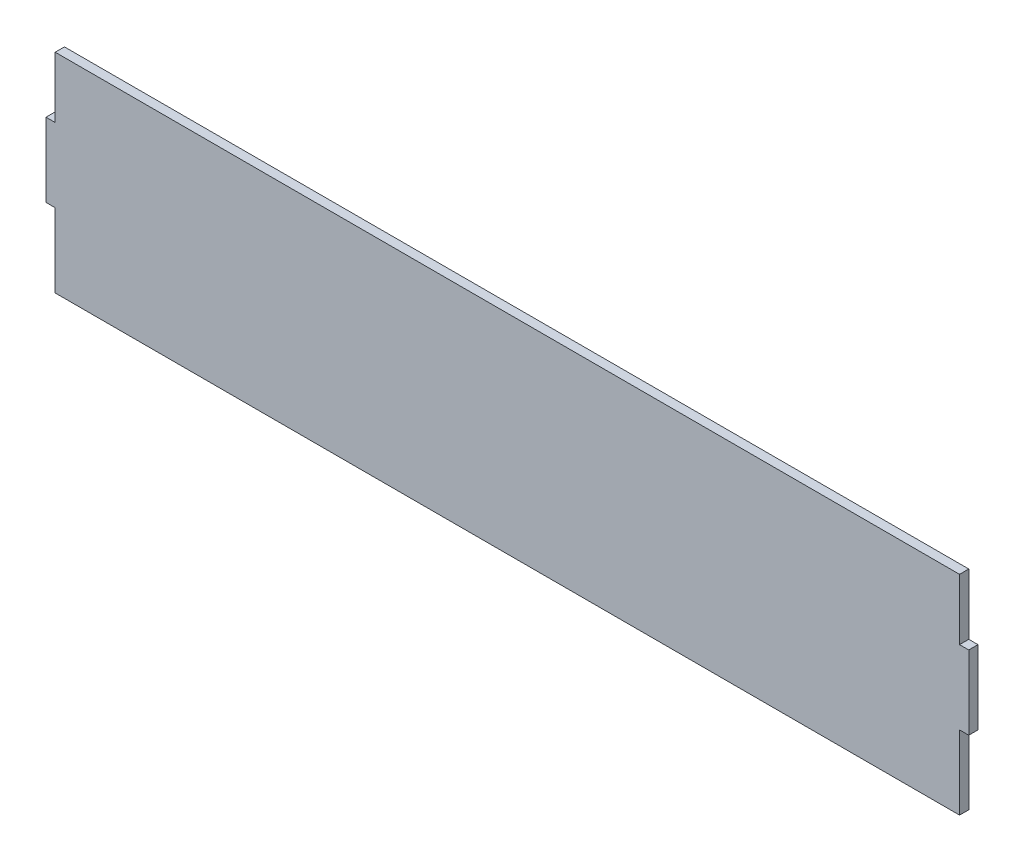
SolidWorks part; units mm, degrees
material "PMMA"
ref_plane "Plan de face" through (0, 0, 0) normal (0, 0, 1) x (1, 0, 0)
ref_plane "Plan de dessus" through (0, 0, 0) normal (0, 1, 0) x (1, 0, 0)
ref_plane "Plan de droite" through (0, 0, 0) normal (1, 0, 0) x (0, 0, -1)
sketch "Esquisse1" plane through (0, 0, 0) normal (0, 0, 1) x (1, 0, 0)
  line L0 (5, 0) -> (5, 40)
  line L1 (5, 0) -> (495, 0)
  line L2 (0, 40) -> (0, 80)
  line L3 (5, 113) -> (495, 113)
  line L5 (5, 40) -> (0, 40)
  line L6 (0, 40) -> (0, 80)
  line L7 (0, 80) -> (5, 80)
  line L8 (5, 80) -> (5, 113)
  line L9 (495, 0) -> (495, 40)
  line L10 (495, 40) -> (500, 40)
  line L11 (500, 80) -> (500, 40)
  line L12 (500, 80) -> (495, 80)
  line L13 (495, 80) -> (495, 113)
  dimension "D1" = 500
  dimension "D2" = 113
  dimension "D3" = 5
  dimension "D4" = 40
  dimension "D5" = 40
  dimension "D6" = 33
  dimension "D7" = 5
extrude "Boss.-Extru.1" add sketch "Esquisse1" along normal blind 5 contours L12 L13 L3 L8 L7 L2 L5 L0 L1 L9 L10 L11
